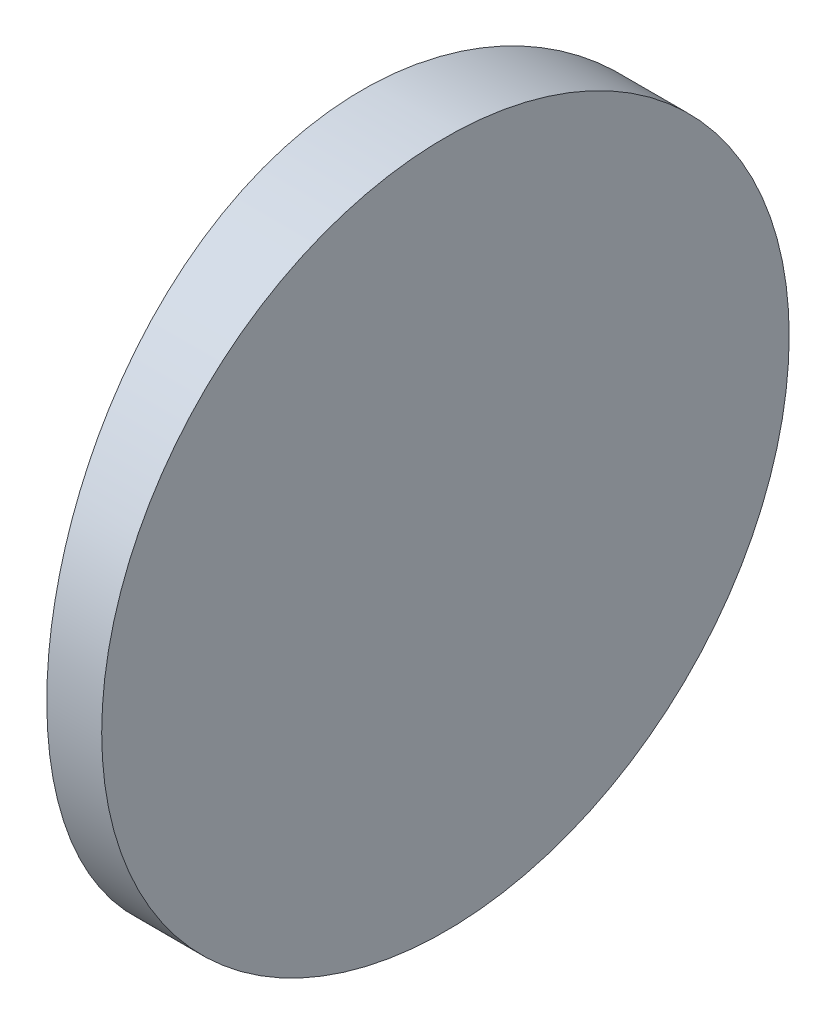
SolidWorks part; units mm, degrees
ref_plane "前视基准面" through (0, 0, 0) normal (0, 0, 1) x (1, 0, 0)
ref_plane "上视基准面" through (0, 0, 0) normal (0, 1, 0) x (1, 0, 0)
ref_plane "右视基准面" through (0, 0, 0) normal (1, 0, 0) x (0, 0, -1)
sketch "草图1" plane through (0, 0, 0) normal (0, 1, 0) x (1, 0, 0)
  line L0 (10.7432, 0) -> (-75.2096, 0) construction
  line L1 (-72.1808, 12.5) -> (-70.1848, 12.5)
  line L2 (-72.1808, -12.5) -> (-70.1848, -12.5)
  line L3 (-70.1848, 12.5) -> (-70.1848, -12.5)
  arc A0 (-72.1808, 12.5) -> (-72.1808, -12.5) centre (4.3552, 0) ccw
  point P19 (-73.1948, 0)
  point P20 (-70.1848, 0)
  dimension "D2" = 12.5
  dimension "D3" = 77.55
  dimension "D4" = 3.01
  dimension "D1" = 12.5
extrude "凸台-拉伸1" add sketch "草图1" along normal blind 25 contours A0 L2 L3 L1
sketch "草图2" plane through (-70.1848, 0, 0) normal (1, 0, 0) x (0, 0, -1)
  line L0 (12.5, 0) -> (-12.5, 0) construction
  line L7 (-12.5, 0) -> (12.5, 0)
  line L8 (12.5, 0) -> (12.5, 25)
  line L9 (12.5, 25) -> (-12.5, 25)
  line L10 (-12.5, 25) -> (-12.5, 0)
  line L11 (-12.5, 0) -> (12.5, 0)
  line L12 (12.5, 0) -> (12.5, 25)
  line L13 (12.5, 25) -> (-12.5, 25)
  line L14 (-12.5, 25) -> (-12.5, 0)
  circle A0 centre (0, 12.5) radius 12.5
  line M1 (-12.5, 0) -> (12.5, 0)
  line M2 (12.5, 0) -> (12.5, 25)
  line M3 (12.5, 25) -> (-12.5, 25)
  line M4 (-12.5, 25) -> (-12.5, 0)
  dimension "D1" = 25
  dimension "D4" = 12.5
  dimension "D2" = 12.5
  dimension "D3" = 0
extrude "切除-拉伸8" cut sketch "草图2" against normal blind 12.7 contours A0 L13 M4 | A0 L12 M3 | A0 L11 M2 | A0 L14 M1
